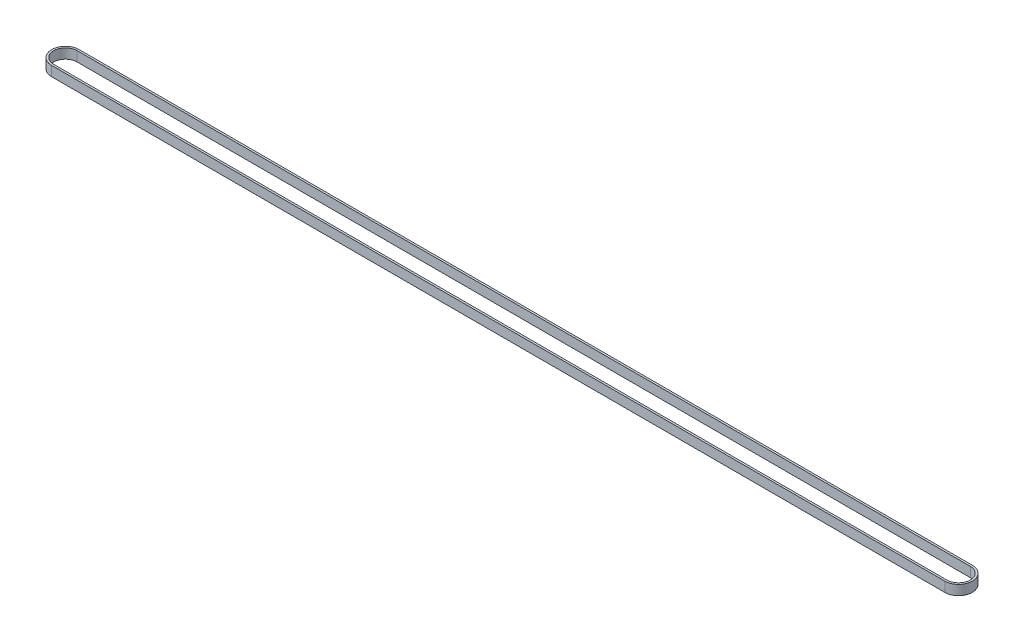
SolidWorks part; units mm, degrees
ref_plane "Plan de face" through (0, 0, 0) normal (0, 0, 1) x (1, 0, 0)
ref_plane "Plan de dessus" through (0, 0, 0) normal (0, 1, 0) x (1, 0, 0)
ref_plane "Plan de droite" through (0, 0, 0) normal (1, 0, 0) x (0, 0, -1)
sketch "Esquisse1" plane through (0, -3570.4509, 0) normal (0, 1, 0) x (1, 0, 0)
  line L0 (-454.86, -6) -> (0, -6)
  line L1 (-425.1759, 0) -> (0, 0) construction
  line L2 (-454.86, -7) -> (0, -7)
  line L3 (-454.86, 6) -> (0, 6)
  line L4 (-454.86, 7) -> (0, 7)
  arc A0 (-454.86, -6) -> (-454.86, 6) centre (-454.86, 0) cw
  arc A3 (0, 6) -> (0, -6) centre (0, 0) cw
  arc A5 (-454.86, 7) -> (-454.86, -7) centre (-454.86, 0) ccw
  arc A6 (0, 7) -> (0, -7) centre (0, 0) cw
  dimension "D1" = 1
  dimension "D3" = 6
  dimension "D4" = 454.86
extrude "Boss.-Extru.1" add sketch "Esquisse1" along normal blind 5
